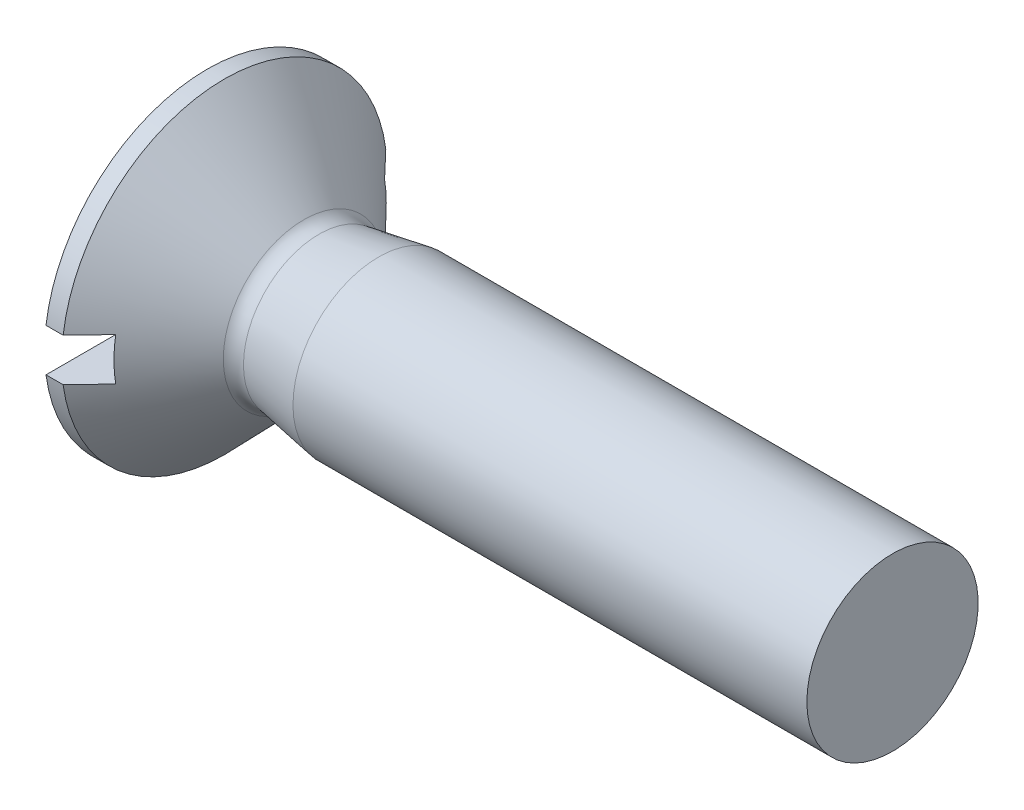
SolidWorks part; units mm, degrees
material "AISI 1020"
ref_plane "Спереди" through (0, 0, 0) normal (0, 0, 1) x (1, 0, 0)
ref_plane "Сверху" through (0, 0, 0) normal (0, 1, 0) x (1, 0, 0)
ref_plane "Справа" through (0, 0, 0) normal (1, 0, 0) x (0, 0, -1)
sketch "Эскиз2" plane through (0, 0, 0) normal (0, 0, 1) x (1, 0, 0)
  line L0 (0, 0) -> (13.7777, 0) construction
  line L3 (0, 0) -> (0, 1.9)
  line L4 (0, 1.9) -> (0.2, 1.9)
  line L5 (0.2, 1.9) -> (1.1267, 0.9403)
  line L6 (1.304, 0.8821) -> (2, 1)
  line L7 (2, 1) -> (8, 1)
  line L8 (8, 1) -> (8, 0)
  line L9 (0, 0) -> (8, 0)
  arc A0 (1.1267, 0.9403) -> (1.304, 0.8821) centre (1.2706, 1.0793) ccw
  point P16 (1.2, 0.8645)
  dimension "D10" = 0.2
  dimension "D2" = 1.9
  dimension "D3" = 0.2
  dimension "D4" = 1
  dimension "D5" = 1.1267
  dimension "D6" = 46
  dimension "D7" = 8
  dimension "D8" = 1.2
  dimension "D9" = 0.8
revolve "Повернуть1" add sketch "Эскиз2" angle 360 about L0
sketch "Эскиз3" plane through (0, 0, 0) normal (0, 0, 1) x (1, 0, 0)
  line L0 (0, 0) -> (14.0195, 0) construction
  line L1 (0, 1.9) -> (0, -1.9) construction
  line L2 (0, 0.25) -> (0.5, 0.25)
  line L3 (0.5, 0.25) -> (0.5, -0.25)
  line L5 (0, -0.25) -> (0, 0.25)
  line L6 (0, -0.25) -> (0.5, -0.25)
  point P8 (0.5, 0)
  dimension "D1" = 0.5
  dimension "D2" = 0.25
extrude "Вырез-Вытянуть1" cut sketch "Эскиз3" against normal through all both and the other way through all
